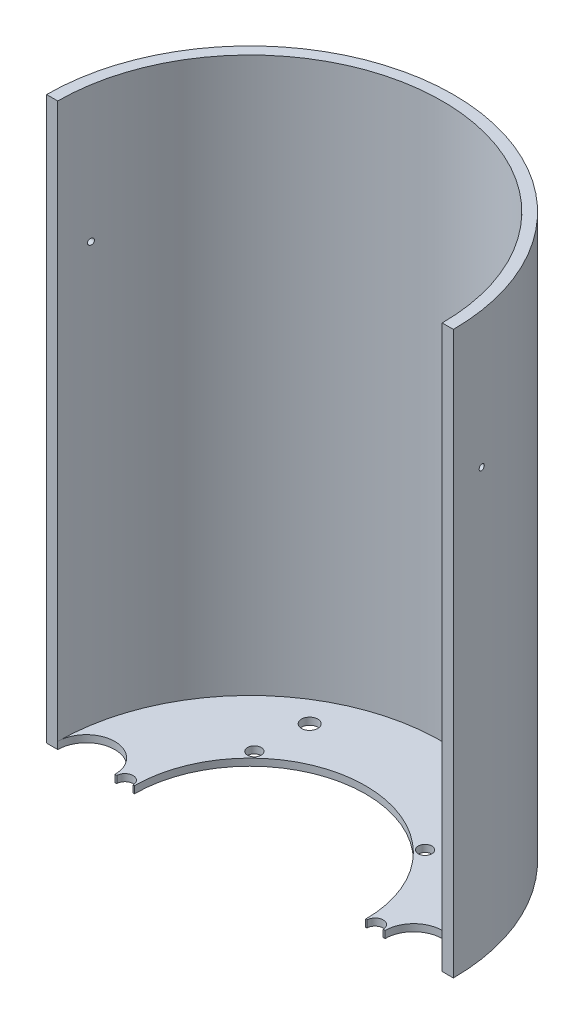
SolidWorks part; units mm, degrees
material "PET"
ref_plane "Front Plane" through (0, 0, 0) normal (0, 0, 1) x (1, 0, 0)
ref_plane "Top Plane" through (0, 0, 0) normal (0, 1, 0) x (1, 0, 0)
ref_plane "Right Plane" through (0, 0, 0) normal (1, 0, 0) x (0, 0, -1)
sketch "Sketch1" plane through (0, 0, 0) normal (0, 1, 0) x (1, 0, 0)
  circle A0 centre (0, 0) radius 94.996
  circle A1 centre (0, 0) radius 53.975
  dimension "D1" = 189.992
  dimension "D2" = 107.95
extrude "Top of Hatch" add sketch "Sketch1" along normal blind 3.302
sketch "Sketch2" plane through (0, 3.302, 0) normal (0, 1, 0) x (1, 0, 0)
  circle A0 centre (0, 0) radius 94.996
  circle A1 centre (0, 0) radius 89.789
  circle A2 centre (0, 0) radius 94.996 construction
  dimension "D1" = 179.578
extrude "Hatch Body" add sketch "Sketch2" along normal blind 259.08
sketch "Sketch3" plane through (0, 0, 0) normal (0, -1, 0) x (1, 0, 0)
  line L0 (0, 0) -> (-76.454, 0) construction
  line L1 (0, 0) -> (0, 76.902) construction
  circle A0 centre (-76.454, 0) radius 13.335
  circle A1 centre (76.454, 0) radius 13.335
  dimension "D1" = 76.454
  dimension "D2" = 26.67
extrude "Charge Tube Holes" cut sketch "Sketch3" against normal through all
sketch "Sketch4" plane through (0, 0, 0) normal (0, -1, 0) x (1, 0, 0)
  line L0 (0, 0) -> (94.996, 0) construction
  line L1 (0, 0) -> (-38.1, -65.9911) construction
  circle A2 centre (-38.1, -65.9911) radius 3.81
  circle A4 centre (0, 0) radius 94.996 construction
  circle A5 centre (-76.2, 0) radius 3.81 [skipped]
  circle A6 centre (-38.1, 65.9911) radius 3.81
  circle A7 centre (38.1, 65.9911) radius 3.81
  circle A8 centre (76.2, 0) radius 3.81 [skipped]
  circle A9 centre (38.1, -65.9911) radius 3.81
  dimension "D1" = 6
  dimension "D9" = 7.62
  dimension "D2" = 76.2
  dimension "D8" = 38.1
extrude "Bolt Holes" cut sketch "Sketch4" against normal through all
sketch "Sketch 5" plane through (0, 0, 0) normal (0, -1, 0) x (1, 0, 0)
  circle A0 centre (-26.1124, 57.3248) radius 5.08
  circle A1 centre (9.1936, 61.0335) radius 5.08
  dimension "D1" = 10.16
  dimension "D2" = 10.16
  dimension "D3" = 62.992
  dimension "D4" = 61.722
  dimension "D5" = 26.1124
  dimension "D6" = 35.306
extrude "Antenna Holes " cut sketch "Sketch 5" against normal through all
sketch "Sketch5" plane through (0, 0, 0) normal (0, -1, 0) x (1, 0, 0)
  line L0 (0, -104.4956) -> (0, 104.4956) construction
  line L2 (104.4956, 0) -> (-104.4956, 0) construction
  circle A0 centre (58.42, 0) radius 3.81
  circle A1 centre (-58.42, 0) radius 3.81
  circle A3 centre (39.878, 41.91) radius 3.175
  circle A4 centre (-39.878, 41.91) radius 3.175
  circle A5 centre (39.878, -41.91) radius 3.175
  circle A6 centre (-39.878, -41.91) radius 3.175
  dimension "D1" = 7.62
  dimension "D3" = 6.35
  dimension "D2" = 58.42
  dimension "D4" = 41.91
  dimension "D5" = 39.878
extrude "Inner Screw Holes" cut sketch "Sketch5" against normal through all
sketch3d "3DSketch3" plane through (0, 0, 0) normal (0, 0, 1) x (1, 0, 0)
  dimension "D1" = 94.996
sketch "Sketch8" plane through (94.996, 0, 0) normal (1, 0, 0) x (0, 0, -1)
  line L0 (0, 0) -> (0, 262.382) construction
  line L1 (94.996, 262.382) -> (-94.996, 262.382) construction
  line L2 (0, 198.882) -> (50000, 198.882) construction
  circle A0 centre (0, 198.882) radius 1.4351 construction
  circle A1 centre (14.351, 198.882) radius 1.397
  circle A2 centre (-14.351, 198.882) radius 1.397
  dimension "D1" = 2.8702
  dimension "D3" = 2.794
  dimension "D2" = 63.5
  dimension "D4" = 14.351
extrude "Cut-Extrude1" cut sketch "Sketch8" against normal through all
sketch "Sketch12" plane through (0, 0, 0) normal (0, -1, 0) x (1, 0, 0)
  line L0 (-94.996, 0) -> (94.996, 0)
  circle A0 centre (0, 0) radius 94.996 construction
  arc A1 (-94.996, 0) -> (94.996, 0) centre (0, 0) cw
extrude "Cut-Extrude3" cut sketch "Sketch12" against normal through all
